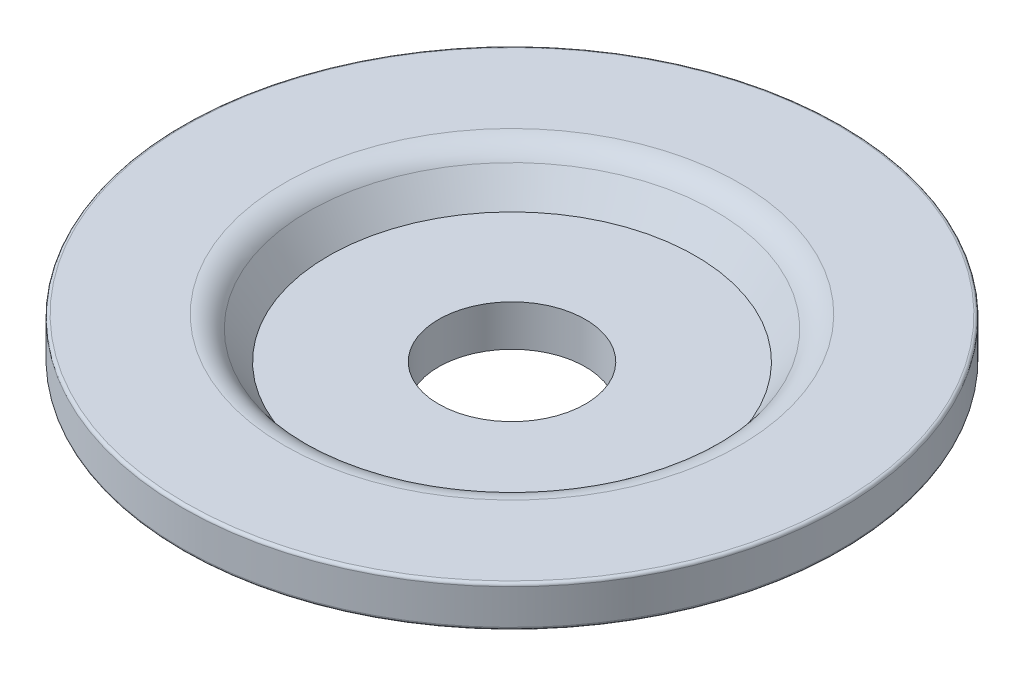
SolidWorks part; units mm, degrees
material "1.0037 (S235JR)"
ref_plane "Front Plane" through (0, 0, 0) normal (0, 0, 1) x (1, 0, 0)
ref_plane "Top Plane" through (0, 0, 0) normal (0, 1, 0) x (1, 0, 0)
ref_plane "Right Plane" through (0, 0, 0) normal (1, 0, 0) x (0, 0, -1)
sketch "Sketch1" plane through (0, 0, 0) normal (0, 0, 1) x (1, 0, 0)
  line L0 (0, -31.3015) -> (0, -41.3015) construction
  line L1 (2.5, 0) -> (6.25, 0)
  line L2 (6.25, 0) -> (6.9305, 0.9731)
  line L3 (7.75, 1.4) -> (11.125, 1.4)
  line L4 (2.5, -1.4) -> (6.1979, -1.4)
  line L5 (7.4271, -0.7596) -> (7.9584, 0)
  line L6 (7.9584, 0) -> (11.125, 0)
  line L7 (11.225, 1.3) -> (11.225, 0.1)
  line L8 (0, -1.4) -> (6.9793, -1.4) construction
  line L9 (6.9793, -1.4) -> (7.9584, 0) construction
  line L10 (7.9584, 0) -> (22.45, 0) construction
  line L11 (7.75, 1.4) -> (22.45, 1.4) construction
  line L12 (2.5, 0) -> (2.5, -1.4)
  line L13 (0, 11.5391) -> (0, -8.5489) construction
  line L15 (0, 0) -> (6.25, 0) construction
  arc A0 (6.9305, 0.9731) -> (7.75, 1.4) centre (7.75, 0.4) cw
  arc A1 (7.9584, 0) -> (7.9584, 0) centre (7.9584, 0) cw
  arc A2 (6.1979, -1.4) -> (7.4271, -0.7596) centre (6.1979, 0.1) ccw
  arc A3 (11.125, 0) -> (11.225, 0.1) centre (11.125, 0.1) ccw
  arc A4 (11.125, 1.4) -> (11.225, 1.3) centre (11.125, 1.3) cw
  point P24 (11.225, 1.4)
  dimension "D1" = 1
  dimension "D7" = 1.5
  dimension "D8" = 0.1
  dimension "D2" = 12.5
  dimension "D3" = 1.4
  dimension "D4" = 15.5
  dimension "D5" = 22.45
  dimension "D9" = 5
  dimension "D10" = 1.4
  dimension "D6" = 1.4
revolve "Revolve1" add sketch "Sketch1" angle 360 about L13
